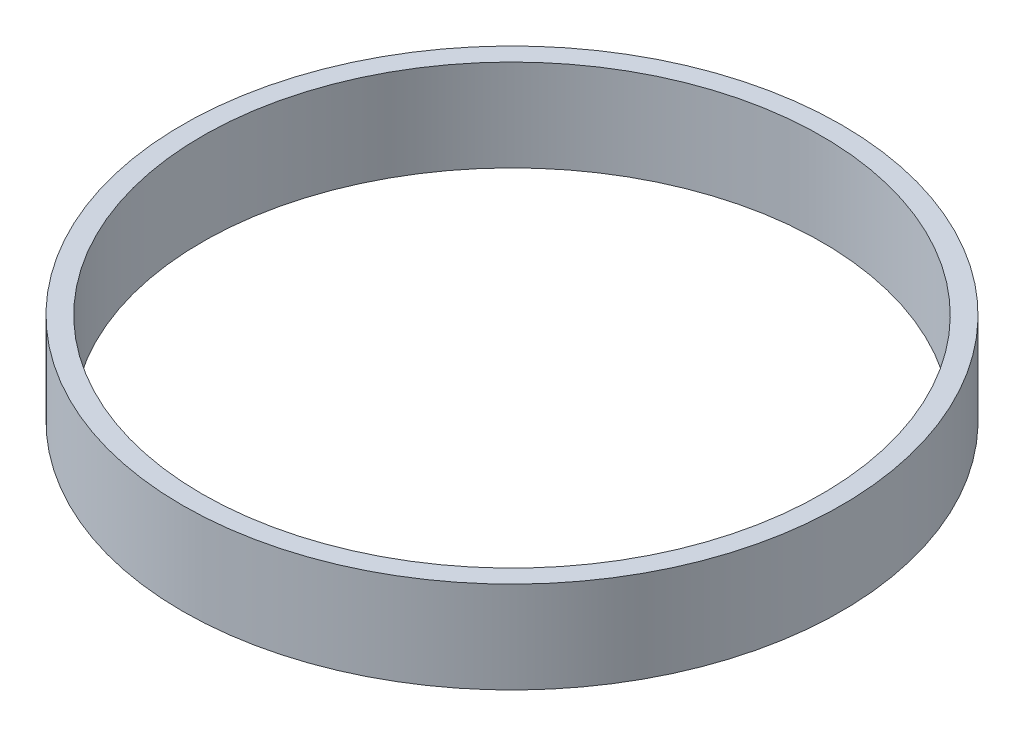
SolidWorks part; units mm, degrees
ref_plane "Front Plane" through (0, 0, 0) normal (0, 0, 1) x (1, 0, 0)
ref_plane "Top Plane" through (0, 0, 0) normal (0, 1, 0) x (1, 0, 0)
ref_plane "Right Plane" through (0, 0, 0) normal (1, 0, 0) x (0, 0, -1)
sketch "Sketch1" plane through (0, 0, 0) normal (0, 1, 0) x (1, 0, 0)
  circle A0 centre (0, 0) radius 79.883
  circle A1 centre (0, 0) radius 75.1205
extrude "Boss-Extrude1" add sketch "Sketch1" along normal blind 22.225
